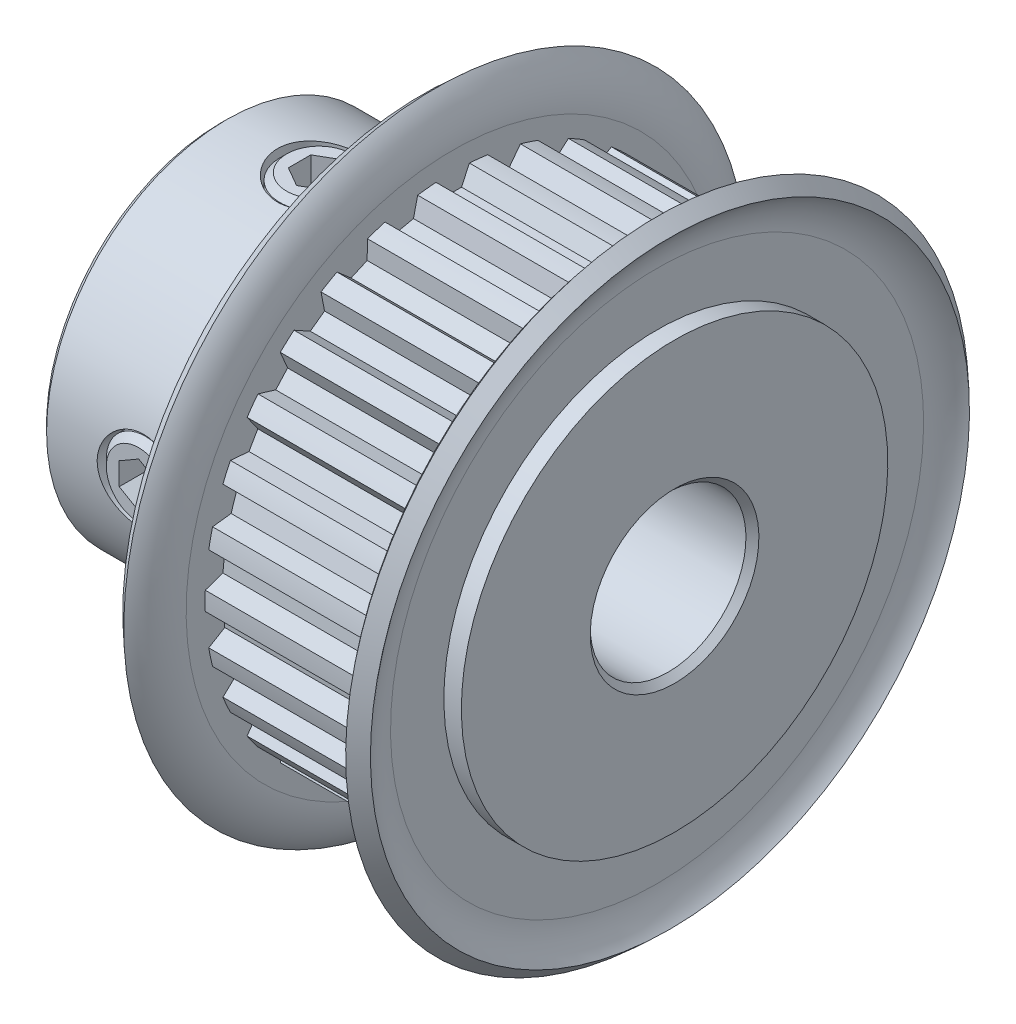
SolidWorks part; units mm, degrees
material "6063-T6"
ref_plane "Front Plane" through (0, 0, 0) normal (0, 0, 1) x (1, 0, 0)
ref_plane "Top Plane" through (0, 0, 0) normal (0, 1, 0) x (1, 0, 0)
ref_plane "Right Plane" through (0, 0, 0) normal (1, 0, 0) x (0, 0, -1)
sketch "Sketch2" plane through (0, 0, 0) normal (1, 0, 0) x (0, 0, -1)
  line L3 (0, 0) -> (0, 8.8745) construction
  line L6 (0, -9.3825) -> (0, -9.7) construction
  line L7 (-0.5715, 9.3651) -> (-0.3397, 8.868)
  line L8 (0.5715, 9.3651) -> (0.3397, 8.868)
  line L9 (-0.5715, 9.3651) -> (-0.6435, 9.5195)
  line L10 (0.5715, 9.3651) -> (0.6435, 9.5195)
  line L12 (-0.3397, 8.868) -> (0.3397, 8.868)
  line L14 (0, 9.3825) -> (0, 9.7) construction
  line L15 (0, 0) -> (0, -1.143) construction
  circle A0 centre (0, 0) radius 9.7 construction
  circle A1 centre (0, 0) radius 8.8745 construction
  circle A2 centre (0, 0) radius 9.3825 construction
  arc A7 (0.6435, 9.5195) -> (-0.6435, 9.5195) centre (0, 0) ccw
  point P5 (0, 9.5412)
  dimension "D3" = 0.3175
  dimension "D1" = 50
sketch "Sketch1" plane through (0, 0, 0) normal (0, 0, 1) x (1, 0, 0)
  line L0 (-8.75, 0) -> (8.75, 0) construction
  line L1 (-8.75, 3) -> (8.75, 3)
  line L2 (-8.75, 3) -> (-8.75, 6.95)
  line L3 (-1.15, 12) -> (-0.475, 12)
  line L4 (0.2, 9.7) -> (0.2, 10.2715)
  line L5 (0.2, 10.843) -> (0.2, 9.7) construction
  line L6 (0.2, 9.7) -> (7.4, 9.7)
  line L7 (7.4, 9.7) -> (7.4, 10.2715)
  line L8 (7.4, 9.7) -> (8.75, 9.7) construction
  line L9 (8.075, 12) -> (8.75, 12)
  line L10 (8.75, 12) -> (8.75, 3)
  line L11 (8.075, 9.7) -> (8.075, 12) construction
  line L12 (-4.95, 6.95) -> (-4.95, 3) construction
  line L13 (-1.15, 12) -> (-1.15, 6.95)
  line L14 (-1.15, 6.95) -> (-8.75, 6.95)
  arc A0 (7.4, 10.2715) -> (8.075, 12) centre (9.9506, 10.2715) cw
  arc A1 (0.2, 10.2715) -> (-0.475, 12) centre (-2.3506, 10.2715) ccw
  point P20 (3.8, 9.7)
  dimension "Bore Size" = 6
  dimension "Overall Width" = 17.5
  dimension "Inside Width" = 7.2
  dimension "OD" = 24
  dimension "D2" = 19.4
  dimension "D3" = 1.143
  dimension "D4" = 0.5715
  dimension "Outside Width" = 9.9
revolve "Revolve1" add sketch "Sketch1" angle 360 mid plane about L0
sketch "Sketch4" plane through (0.2, 0, 0) normal (1, 0, 0) x (0, 0, -1)
  circle A0 centre (0, 0) radius 9.5412
  circle A2 centre (0, 0) radius 9.7
  circle A3 centre (0, 0) radius 9.7 construction
extrude "Cut-Extrude2" cut sketch "Sketch4" along normal up to surface (7.2 mm away) up to face at (7.4, -9.7, 0)
sketch "Sketch3" plane through (0.2, 0, 0) normal (1, 0, 0) x (0, 0, -1)
  line L2 (-0.5715, 9.3651) -> (-0.3397, 8.868) construction
  line L3 (-0.3397, 8.868) -> (0.3397, 8.868) construction
  line L4 (0.5715, 9.3651) -> (0.3397, 8.868) construction
  line L5 (-0.6435, 9.5195) -> (-0.3397, 8.868)
  line L6 (-0.3397, 8.868) -> (0.3397, 8.868)
  line L7 (0.6435, 9.5195) -> (0.3397, 8.868)
  arc A1 (0.6435, 9.5195) -> (-0.6435, 9.5195) centre (0, 0) ccw construction
  arc A2 (0.6435, 9.5195) -> (-0.6435, 9.5195) centre (0, 0) ccw
extrude "Cut-Extrude1" cut sketch "Sketch3" along normal up to surface (7.2 mm away)
pattern_circular "CirPattern1" count 30 over 360 about axis through (0, 0, 0) along (1, 0, 0) of "Cut-Extrude1"
sketch "Sketch6" plane through (0, 0, 0) normal (0, 1, 0) x (1, 0, 0)
  line L0 (-8.75, 0) -> (-6.45, 0) construction
  line L2 (-1.15, 0) -> (-3.45, 0) construction
  line L5 (-4.95, 0) -> (-6.0107, -1.0607) construction
  circle A0 centre (-4.95, 0) radius 1.5 construction
  circle A1 centre (-4.95, 0) radius 1.6
  dimension "D1" = 0.1
  dimension "D2" = 45
  dimension "SS Dia" = 3
extrude "Cut-Extrude3" cut sketch "Sketch6" along normal through all
sketch "Sketch7" plane through (0, 0, 0) normal (0, 0, 1) x (1, 0, 0)
  line L0 (-6.196, 6.95) -> (-4.95, 6.95)
  line L1 (-6.45, 6.696) -> (-6.45, 3.635)
  line L2 (-6.45, 3.635) -> (-6.196, 3.381)
  line L3 (-6.196, 3.381) -> (-4.95, 3.381)
  line L4 (-4.95, 3.381) -> (-4.95, 6.95) construction
  line L5 (-1.15, 6.95) -> (-8.75, 6.95) construction
  line L6 (-6.45, 6.696) -> (-6.196, 6.95)
  line L8 (-4.95, 6.95) -> (-4.95, 3.381)
  point P0 (-6.45, 6.95)
  point P4 (-6.45, 3.381)
  dimension "D2" = 0.381
revolve "Revolve2" add sketch "Sketch7" angle 360 mid plane about L4
sketch "Sketch8" plane through (0, 6.95, 0) normal (0, 1, 0) x (1, 0, 0)
  line L0 (-4.95, 0) -> (-4.95, 1.5) construction
  line L1 (-4.95, 0.866) -> (-5.7, 0.433)
  line L2 (-5.7, 0.433) -> (-5.7, -0.433)
  line L3 (-5.7, -0.433) -> (-4.95, -0.866)
  line L4 (-4.95, -0.866) -> (-4.2, -0.433)
  line L5 (-4.2, -0.433) -> (-4.2, 0.433)
  line L6 (-4.2, 0.433) -> (-4.95, 0.866)
  circle A0 centre (-4.95, 0) radius 0.75 construction
  circle A1 centre (-4.95, 0) radius 1.5 construction
  point P16 (-4.95, 0.75)
extrude "Cut-Extrude4" cut sketch "Sketch8" against normal blind 1.016
pattern_circular "CirPattern2" count 2 over 90 about axis through (-8.75, 0, 0) along (-1, 0, 0) of "Cut-Extrude3"
pattern_circular "CirPattern3" count 2 over 90 about axis through (0, 0, 0) along (1, 0, 0) of bodies 107
sketch "Sketch5" plane through (0, 0, 0) normal (0, 0, 1) x (1, 0, 0)
  line L1 (7.4, 10.2715) -> (7.4, -10.2715) construction
  line L5 (0.2, -10.2715) -> (0.2, 10.2715) construction
  line L6 (0.2, -10.2715) -> (0.2, 10.2715) construction
  line L7 (7.4, 10.2715) -> (7.4, -10.2715) construction
  line L8 (-6.45, 0) -> (-4.95, 0) construction
  line L9 (-4.95, 0) -> (-6.0107, -1.0607) construction
  circle A0 centre (-4.95, 0) radius 1.5 construction
  circle A1 centre (-4.95, 0) radius 1.5 construction
  point P0 (7.4, 0)
  point P10 (-6.0107, -1.0607)
  dimension "D1" = 45
sketch "Sketch10" plane through (0, 0, 0) normal (0, 1, 0) x (1, 0, 0)
  line L0 (-1.15, 12) -> (-1.15, -12) construction
  line L1 (-1.15, 12) -> (-1.15, -12)
chamfer "Chamfer1" distance 0.25 angle 45 3 edges at (-8.75, -6.95, 0) (8.75, -3, 0) (-8.75, -3, 0)
sketch "Sketch9" plane through (0, 0, 0) normal (0, 0, 1) x (1, 0, 0)
  line L0 (-8.75, 0) -> (8.75, 0) construction
  line L3 (8.075, 12) -> (8.5714, 11.5426)
  line L4 (8.075, 10.2715) -> (8.075, 8.2165)
  line L5 (0.2, 8.2165) -> (8.075, 8.2165) construction
  line L6 (8.075, 8.2165) -> (8.75, 8.2165)
  line L7 (8.75, 12) -> (8.75, 3) construction
  line L8 (8.75, 8.2165) -> (8.75, 12)
  line L9 (8.075, 12) -> (8.385, 12.3364)
  line L10 (8.385, 12.3364) -> (8.75, 12)
  line L11 (0.2, 9.5195) -> (0.2, 8.868) construction
  line L12 (0.2, 8.868) -> (0.2, 8.2165) construction
  arc A0 (8.5714, 11.5426) -> (8.075, 10.2715) centre (9.9506, 10.2715) ccw
  arc A2 (8.075, 12) -> (7.4, 10.2715) centre (9.9506, 10.2715) ccw construction
revolve "Cut-Revolve1" cut sketch "Sketch9" angle 360 about L0
ref_plane "Plane1" through (3.8, 0, 0) normal (1, 0, 0) x (0, 0, -1)
mirror "Mirror1" about plane through (3.8, 0, 0) normal (1, 0, 0) of "Cut-Revolve1"
equation "\"D3@Sketch2\" = (\"hs@Sketch2\"-\"ht@Sketch2\")/2"
equation "\"D2@Sketch1\" = \"PD@Sketch2\""
equation "\"D3@Sketch1\" = \"hs@Sketch2\""
equation "\"D4@Sketch1\" = \"D3@Sketch1\"/2"
